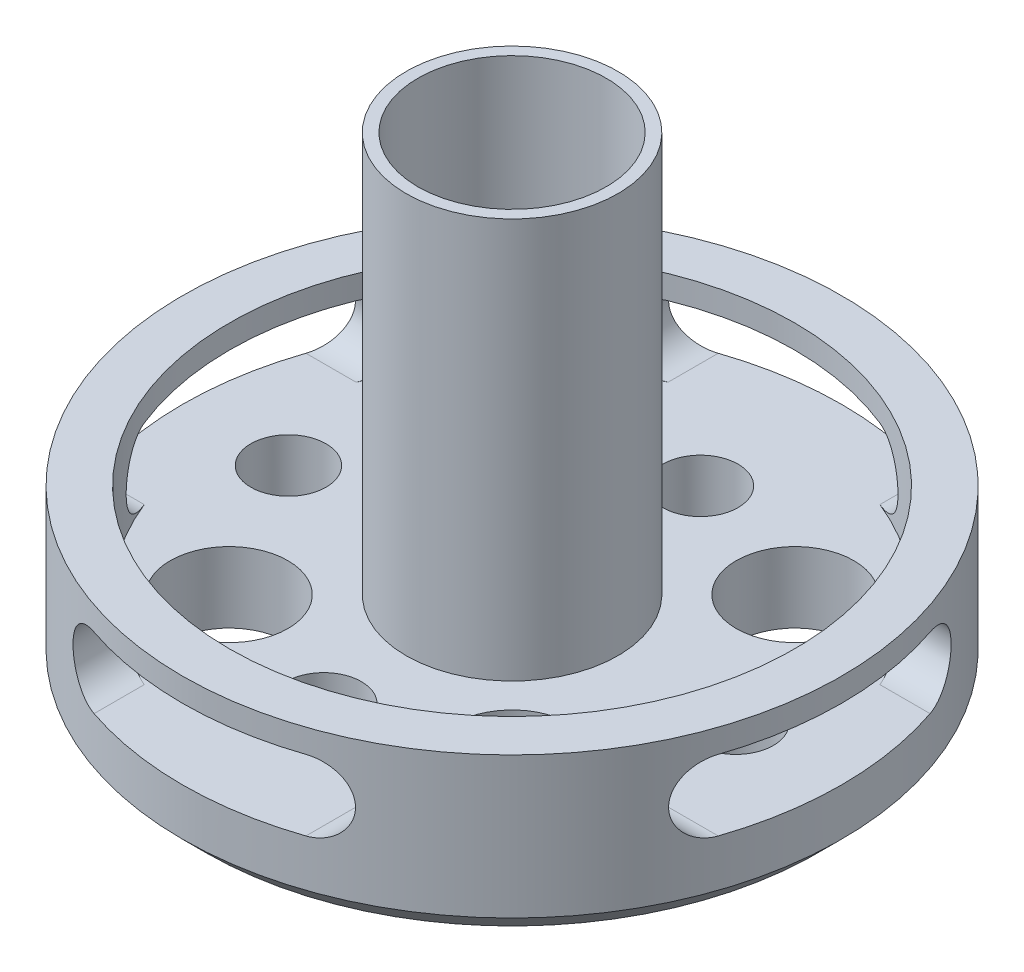
SolidWorks part; units mm, degrees
material "Cast Stainless Steel"
ref_plane "Front Plane" through (0, 0, 0) normal (0, 0, 1) x (1, 0, 0)
ref_plane "Top Plane" through (0, 0, 0) normal (0, 1, 0) x (1, 0, 0)
ref_plane "Right Plane" through (0, 0, 0) normal (1, 0, 0) x (0, 0, -1)
sketch "Sketch1" plane through (0, 0, 0) normal (0, 1, 0) x (1, 0, 0)
  circle A0 centre (0, 0) radius 14
  dimension "D1" = 28
extrude "Boss-Extrude1" add sketch "Sketch1" along normal blind 7
chamfer "Chamfer1" distance 1 angle 45 1 edges at (0, 0, 14)
sketch "Sketch11" plane through (0, 7, 0) normal (0, 1, 0) x (1, 0, 0)
  circle A0 centre (0, 0) radius 12
  circle A1 centre (0, 0) radius 14 construction
  dimension "D1" = 2
extrude "Cut-Extrude3" cut sketch "Sketch11" against normal blind 4
sketch "Sketch2" plane through (0, 0, 0) normal (0, -1, 0) x (1, 0, 0)
  line L0 (0, 13) -> (0, -13) construction
  line L1 (-13, 0) -> (13, 0) construction
  line L2 (-9.1924, 9.1924) -> (9.1924, -9.1924) construction
  line L3 (-9.1924, -9.1924) -> (9.1924, 9.1924) construction
  circle A0 centre (0, 0) radius 13 construction
  circle A1 centre (0, 0) radius 4
  circle A2 centre (6.0104, 6.0104) radius 2.5
  circle A3 centre (6.0104, -6.0104) radius 2.5
  circle A4 centre (-6.0104, -6.0104) radius 2.5
  circle A5 centre (-6.0104, 6.0104) radius 2.5
  point P25 (0, 0)
  dimension "D3" = 8
  dimension "D4" = 5
  dimension "D5" = 4.5
  dimension "D1" = 45
  dimension "D2" = 45
  dimension "D6" = 4
hole_wizard "M3 Clearance Hole2" positions "Sketch4" profile "Sketch3" hole size "M3" standard "ISO" end condition through all
sketch "Sketch4" plane through (0, 0, 0) normal (0, -1, 0) x (-1, 0, 0)
  line L0 (13, 0) -> (-13, 0) construction
  point P0 (9.5, 0)
  point P4 (-9.5, 0)
  point P6 (0, 8)
  point P8 (0, -8)
  dimension "D1" = 8
  dimension "D3" = 3.5
  dimension "D4" = 3.5
  dimension "D5" = 16
sketch "Sketch3" plane through (-9.5, 0, 0) normal (1, 0, 0) x (0, 0, -1)
  line L0 (0, 0) -> (0, 7)
  line L1 (0, 7) -> (1.6, 7)
  line L2 (1.6, 7) -> (1.6, 0)
  line L5 (1.6, 0) -> (0, 0)
  line L11 (0, -6.35) -> (0, 107.95) construction
  dimension "Thru Hole Dia." = 3.2
  dimension "Thru Hole Depth" = 7
extrude "Cut-Extrude4" cut sketch "Sketch2" against normal up to surface (3 mm away) up to face at (-9.5, 3, 1.6)
chamfer "Chamfer2" distance 0.5 angle 45 1 edges at (0, 0, -4)
sketch "Sketch10" plane through (0, 0, 0) normal (1, 0, 0) x (0, 0, -1)
  line L1 (-4.5, 6) -> (4.5, 6)
  line L3 (-4.5, 3) -> (4.5, 3)
  line L4 (4, 3) -> (-4, 3) construction
  arc A0 (-4.5, 6) -> (-4.5, 3) centre (-4.5, 4.5) ccw
  arc A1 (4.5, 3) -> (4.5, 6) centre (4.5, 4.5) ccw
  point P6 (0, 3)
  dimension "D3" = 1.5
  dimension "D4" = 1.5
  dimension "D1" = 3
  dimension "D5" = 9
extrude "Cut-Extrude2" cut sketch "Sketch10" against normal blind 14
pattern_circular "CirPattern1" count 4 over 360 about axis through (0, 3, 0) along (0, 1, 0) of "Cut-Extrude2"
sketch "Sketch12" plane through (0, 3, 0) normal (0, 1, 0) x (1, 0, 0)
  circle A0 centre (0, 0) radius 4.5
  circle A1 centre (0, 0) radius 4
  dimension "D1" = 9
extrude "Boss-Extrude3" add sketch "Sketch12" along normal blind 17
